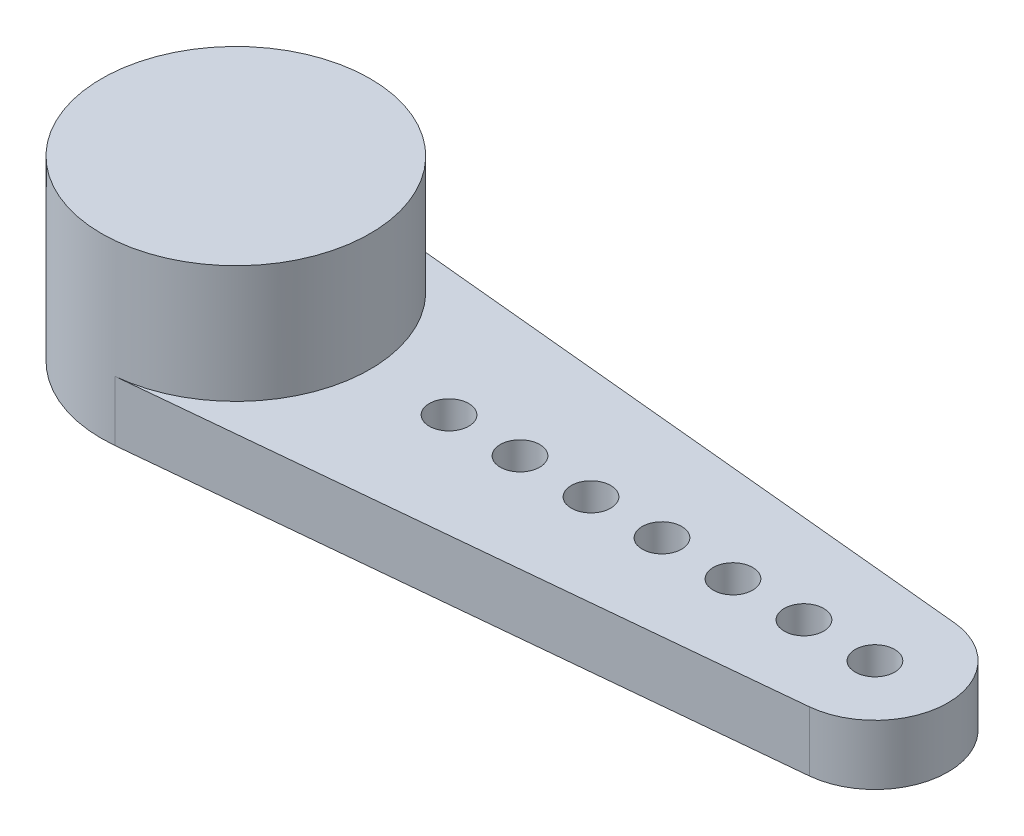
SolidWorks part; units mm, degrees
ref_plane "前视基准面" through (0, 0, 0) normal (0, 0, 1) x (1, 0, 0)
ref_plane "上视基准面" through (0, 0, 0) normal (0, 1, 0) x (1, 0, 0)
ref_plane "右视基准面" through (0, 0, 0) normal (1, 0, 0) x (0, 0, -1)
sketch "草图1" plane through (0, 0, 0) normal (0, 1, 0) x (1, 0, 0)
  circle A0 centre (0, 0) radius 3.405
  dimension "D1" = 6.81
extrude "凸台-拉伸1" add sketch "草图1" along normal blind 4.5
sketch "草图2" plane through (0, 0, 0) normal (0, -1, 0) x (1, 0, 0)
  line L0 (0, 0) -> (18.055, 0) construction
  line L1 (-3.405, 4.6297) -> (-3.405, -5.36) construction
  line L2 (0.3267, 3.3893) -> (16.3825, 1.8415)
  line L3 (0.3267, -3.3893) -> (16.3825, -1.8415)
  arc A0 (16.3825, -1.8415) -> (16.3825, 1.8415) centre (16.205, 0) ccw
  circle A1 centre (0, 0) radius 3.405
  arc A2 (0.3267, 3.3893) -> (0.3267, -3.3893) centre (0, 0) ccw
  dimension "D3" = 3.7
  dimension "D2" = 21.46
  dimension "D1" = 0
extrude "凸台-拉伸2" add sketch "草图2" against normal blind 1.52
sketch "草图3" plane through (0, 0, 0) normal (0, -1, 0) x (1, 0, 0)
  circle A0 centre (16.205, 0) radius 0.5
  circle A1 centre (14.405, 0) radius 0.5
  circle A2 centre (12.605, 0) radius 0.5
  circle A3 centre (10.805, 0) radius 0.5
  circle A4 centre (9.005, 0) radius 0.5
  circle A5 centre (7.205, 0) radius 0.5
  circle A6 centre (5.405, 0) radius 0.5
  dimension "D1" = 1
  dimension "D2" = 7
extrude "切除-拉伸1" cut sketch "草图3" against normal blind 1.52
